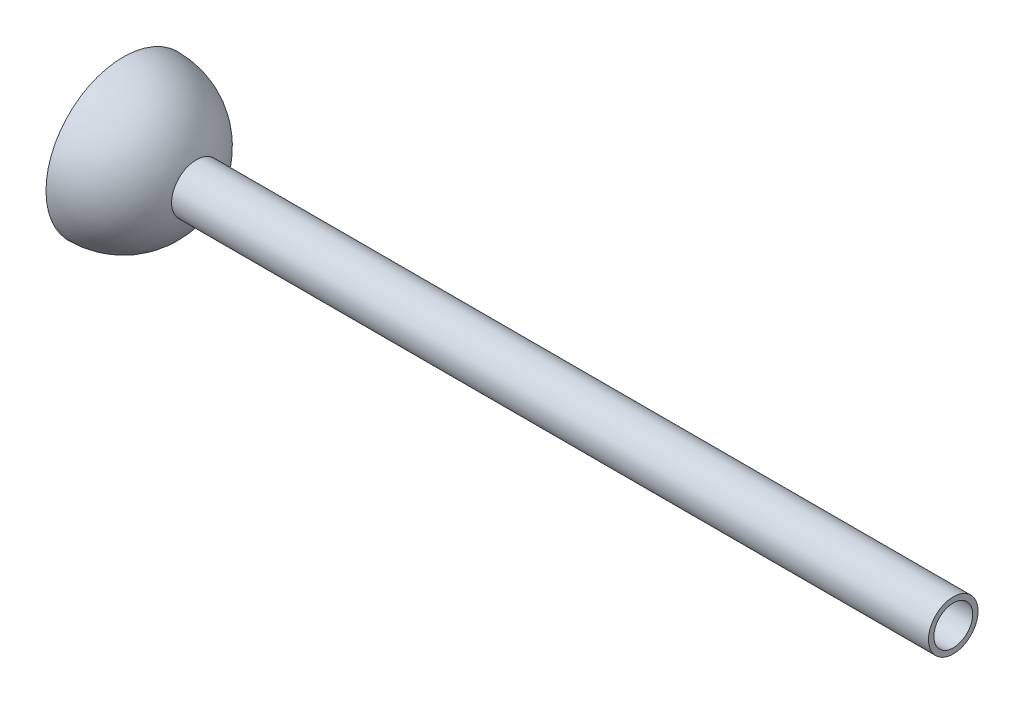
SolidWorks part; units mm, degrees
ref_plane "Front Plane" through (0, 0, 0) normal (0, 0, 1) x (1, 0, 0)
ref_plane "Top Plane" through (0, 0, 0) normal (0, 1, 0) x (1, 0, 0)
ref_plane "Right Plane" through (0, 0, 0) normal (1, 0, 0) x (0, 0, -1)
sketch "Sketch1" plane through (0, 0, 0) normal (0, 1, 0) x (1, 0, 0)
  line L0 (0, 0) -> (17.5462, 0) construction
  line L1 (0, 12.7) -> (0, 10.795)
  line L2 (12.0287, 4.0743) -> (136.525, 4.0743)
  line L3 (10.795, 0) -> (12.7, 0)
  line L4 (12.292, 3.1933) -> (136.525, 3.1933)
  line L5 (136.525, 4.0743) -> (136.525, 3.1933)
  arc A0 (10.795, 0) -> (0, 10.795) centre (0, 0) ccw
  arc A1 (12.7, 0) -> (12.292, 3.1933) centre (0, 0) ccw
  arc A2 (12.0287, 4.0743) -> (0, 12.7) centre (0, 0) ccw
  point P6 (0, 0)
  dimension "D1" = 25.4
  dimension "D2" = 21.59
  dimension "D3" = 136.525
revolve "Revolve1" add sketch "Sketch1" angle 360 about L0
